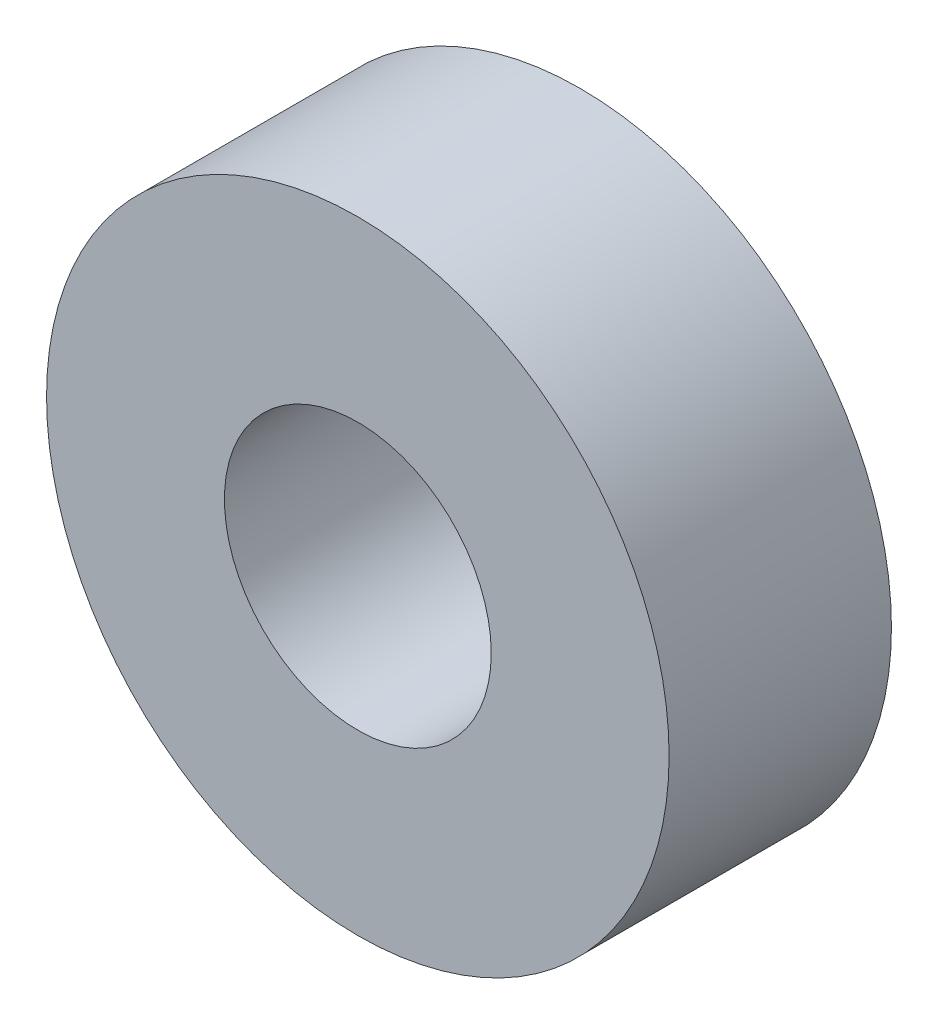
SolidWorks part; units mm, degrees
material "铍红铜, UNS C17000"
ref_plane "前视基准面" through (0, 0, 0) normal (0, 0, 1) x (1, 0, 0)
ref_plane "上视基准面" through (0, 0, 0) normal (0, 1, 0) x (1, 0, 0)
ref_plane "右视基准面" through (0, 0, 0) normal (1, 0, 0) x (0, 0, -1)
other "Configuration Table"
sketch "草图1" plane through (0, 0, 0) normal (0, 0, 1) x (1, 0, 0)
  circle A0 centre (0, 0) radius 3
  circle A1 centre (0, 0) radius 7
  dimension "D1" = 6
  dimension "D2" = 14
extrude "凸台-拉伸1" add sketch "草图1" along normal mid plane 5
